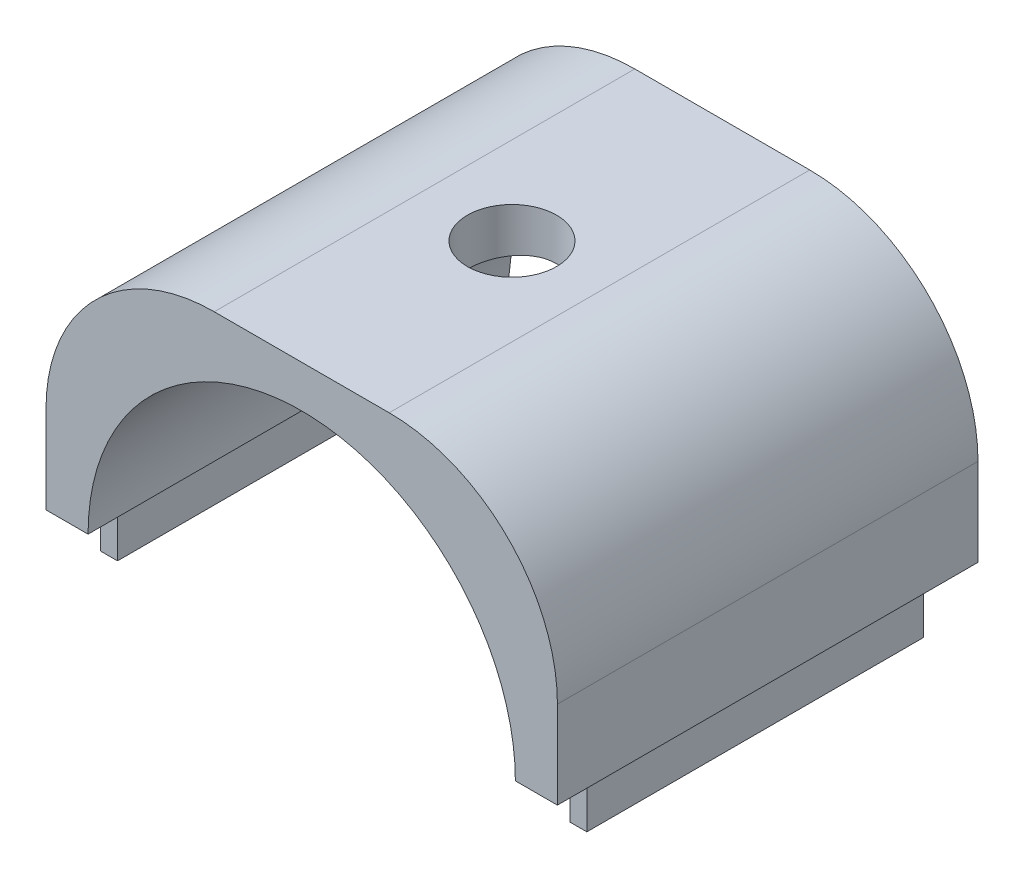
SolidWorks part; units mm, degrees
material "1060 Alloy"
ref_plane "Front Plane" through (0, 0, 0) normal (0, 0, 1) x (1, 0, 0)
ref_plane "Top Plane" through (0, 0, 0) normal (0, 1, 0) x (1, 0, 0)
ref_plane "Right Plane" through (0, 0, 0) normal (1, 0, 0) x (0, 0, -1)
sketch "Sketch1" plane through (0, 0, 0) normal (0, 0, 1) x (1, 0, 0)
  line L0 (-15.2, 0) -> (-12.7, 0)
  line L2 (15.2, 0) -> (15.2, 5.2)
  line L3 (5.2, 15.2) -> (-5.2, 15.2)
  line L4 (-15.2, 0) -> (-15.2, 5.2)
  line L5 (15.2, -15.2) -> (-15.2, 15.2) construction
  line L6 (15.2, 15.2) -> (-15.2, -15.2) construction
  line L7 (12.7, 0) -> (15.2, 0)
  line L8 (-12.7, 0) -> (0, 0) construction
  line L9 (0, 0) -> (12.7, 0) construction
  arc A0 (12.7, 0) -> (-12.7, 0) centre (0, 0) ccw
  arc A2 (15.2, 5.2) -> (5.2, 15.2) centre (5.2, 5.2) ccw
  arc A5 (-5.2, 15.2) -> (-15.2, 5.2) centre (-5.2, 5.2) ccw
  point P1 (0, 15.2)
  dimension "D1" = 25.4
  dimension "D2" = 10
  dimension "D4" = 30.4
  dimension "D3" = 15.2
extrude "Boss-Extrude1" add sketch "Sketch1" along normal mid plane 25
hole_wizard "M5 Clearance Hole1" positions "Sketch2" profile "Sketch3" hole size "M5" standard "ANSI Metric" end condition through all
sketch "Sketch2" plane through (0, 15.2, 0) normal (0, 1, 0) x (1, 0, 0)
  point P0 (0, 0)
sketch "Sketch3" plane through (0, 15.2, 0) normal (1, 0, 0) x (0, 0, 1)
  line L0 (0, 0) -> (0, 15.2)
  line L1 (0, 15.2) -> (2.65, 15.2)
  line L2 (2.65, 15.2) -> (2.65, 0)
  line L5 (2.65, 0) -> (0, 0)
  line L11 (0, -6.35) -> (0, 107.95) construction
  dimension "Thru Hole Dia." = 5.3
  dimension "Thru Hole Depth" = 15.2
sketch "Sketch4" plane through (0, 0, 0) normal (0, -1, 0) x (1, 0, 0)
  line L0 (-13.95, 0) -> (-15.2, 0) construction
  line L1 (-14.45, -10) -> (-13.45, -10)
  line L2 (-14.45, -10) -> (-14.45, 10)
  line L3 (-14.45, 10) -> (-13.45, 10)
  line L4 (-13.45, -10) -> (-13.45, 10)
  line L5 (-14.45, -10) -> (-13.45, 10) construction
  line L6 (-14.45, 10) -> (-13.45, -10) construction
  line L7 (-15.2, 12.5) -> (-15.2, -12.5) construction
  line L8 (-13.95, 0) -> (-12.7, 0) construction
  line L9 (-12.7, 12.5) -> (-12.7, -12.5) construction
  line L10 (0, 10.8415) -> (0, -9.0344) construction
  line L11 (14.45, -10) -> (13.45, -10)
  line L12 (14.45, -10) -> (14.45, 10)
  line L13 (14.45, 10) -> (13.45, 10)
  line L14 (13.45, -10) -> (13.45, 10)
  point P0 (-13.95, 0)
  dimension "D1" = 20
  dimension "D2" = 1
extrude "Boss-Extrude2" add sketch "Sketch4" along normal blind 3
equation "\"keelOutDiameter\"= 1in"
equation "\"keelInDiameter\"= \"keelOutDiameter\" - 0.125in"
equation "\"frontBoltClearance\"= 7.25mm"
equation "\"betweenBoltsDistance\"= 20mm"
equation "\"wingLength\"= 1.4m"
equation "\"frontTubeLength\"= \"wingLength\" / sin ( 34.95deg )"
equation "\"plateThickness\"= 5mm"
equation "\"crossBarOutDiameter\"= 1in"
equation "\"crossBarInDiameter\"= \"crossBarOutDiameter\" - 0.125in"
equation "\"frontToCrossBar\"= 466mm"
equation "\"D1@Sketch1\"=\"keelOutDiameter\""
equation "\"D4@Sketch1\"=\"keelOutDiameter\"+5mm"
equation "\"D3@Sketch1\"=\"keelOutDiameter\"/2+2.5"
